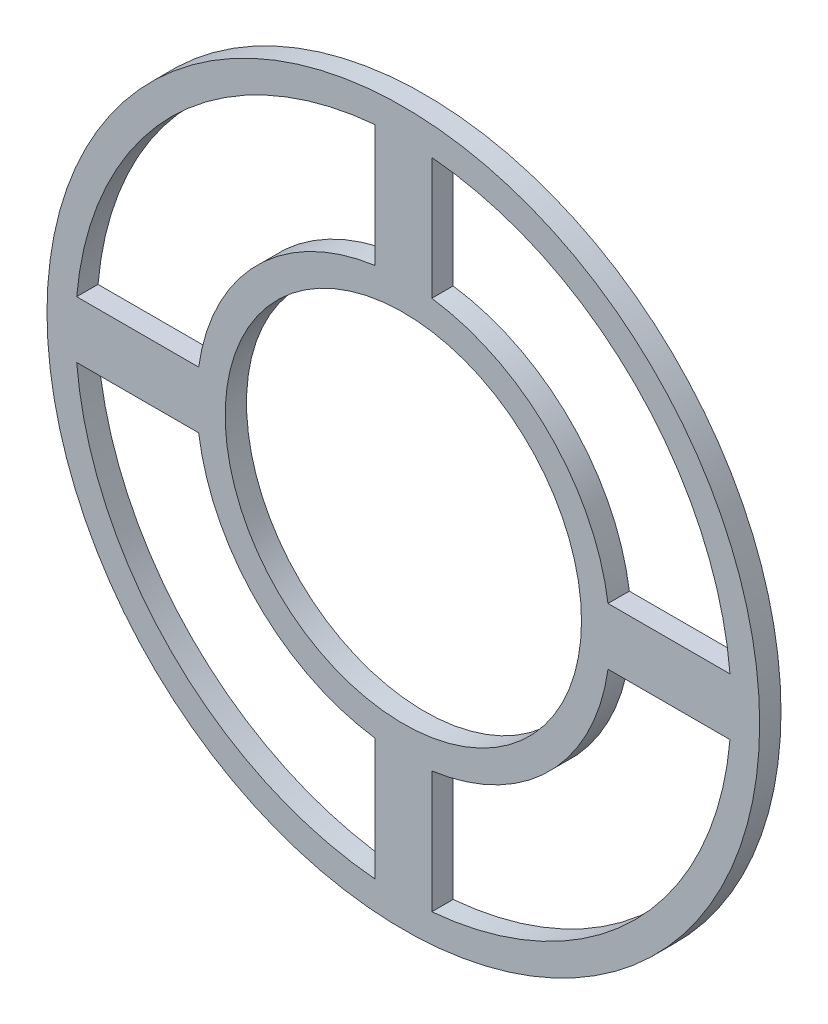
SolidWorks part; units mm, degrees
ref_plane "Front Plane" through (0, 0, 0) normal (0, 0, 1) x (1, 0, 0)
ref_plane "Top Plane" through (0, 0, 0) normal (0, 1, 0) x (1, 0, 0)
ref_plane "Right Plane" through (0, 0, 0) normal (1, 0, 0) x (0, 0, -1)
sketch "Sketch1" plane through (0, 0, 0) normal (0, 0, 1) x (1, 0, 0)
  line L0 (-6.35, 45.6616) -> (-6.35, 72.8759)
  line L1 (6.35, 45.6616) -> (6.35, 72.8759)
  line L3 (-45.6616, 6.35) -> (-72.8759, 6.35)
  line L4 (-45.6616, -6.35) -> (-72.8759, -6.35)
  line L5 (-6.35, -45.6616) -> (-6.35, -72.8759)
  line L6 (6.35, -45.6616) -> (6.35, -72.8759)
  line L7 (45.6616, 6.35) -> (72.8759, 6.35)
  line L8 (45.6616, -6.35) -> (72.8759, -6.35)
  circle A0 centre (0, 0) radius 39.751
  circle A1 centre (0, 0) radius 79.502
  arc A2 (-6.35, 72.8759) -> (-72.8759, 6.35) centre (0, 0) ccw
  arc A3 (-6.35, 45.6616) -> (-45.6616, 6.35) centre (0, 0) ccw
  arc A4 (-45.6616, -6.35) -> (-6.35, -45.6616) centre (0, 0) ccw
  arc A5 (6.35, -45.6616) -> (45.6616, -6.35) centre (0, 0) ccw
  arc A6 (6.35, -72.8759) -> (6.35, 72.8759) centre (0, 0) ccw
  arc A7 (45.6616, 6.35) -> (6.35, 45.6616) centre (0, 0) ccw
  arc A8 (-72.8759, -6.35) -> (-6.35, -72.8759) centre (0, 0) ccw
  dimension "D1" = 79.502
  dimension "D2" = 159.004
  dimension "D4" = 6.35
  dimension "D5" = 6.35
  dimension "D3" = 12.7
extrude "Boss-Extrude1" add sketch "Sketch1" along normal blind 4.7625
